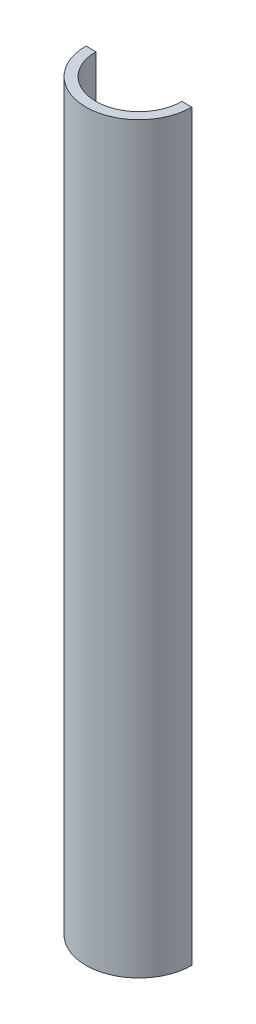
SolidWorks part; units mm, degrees
ref_plane "Front Plane" through (0, 0, 0) normal (0, 0, 1) x (1, 0, 0)
ref_plane "Top Plane" through (0, 0, 0) normal (0, 1, 0) x (1, 0, 0)
ref_plane "Right Plane" through (0, 0, 0) normal (1, 0, 0) x (0, 0, -1)
sketch "Sketch2" plane through (0, 0, 0) normal (0, 1, 0) x (1, 0, 0)
  circle A0 centre (0, 0) radius 21.36
  dimension "D1" = 42.72
extrude "Boss-Extrude1" add sketch "Sketch2" along normal blind 300
shell "Shell1" thickness 4
sketch "Sketch3" plane through (0, 0, 0) normal (1, 0, 0) x (0, 0, -1)
  line L0 (0, 23.496) -> (0, -23.496) construction
  line L1 (0, 316.589) -> (54.4623, 316.589)
  line L2 (0, 316.589) -> (0, -40.436)
  line L3 (0, -40.436) -> (54.4623, -40.436)
  line L4 (54.4623, 316.589) -> (54.4623, -40.436)
  point P6 (0, 316.589)
  point P7 (0, -40.436)
extrude "Cut-Extrude1" cut sketch "Sketch3" against normal through all both and the other way through all
